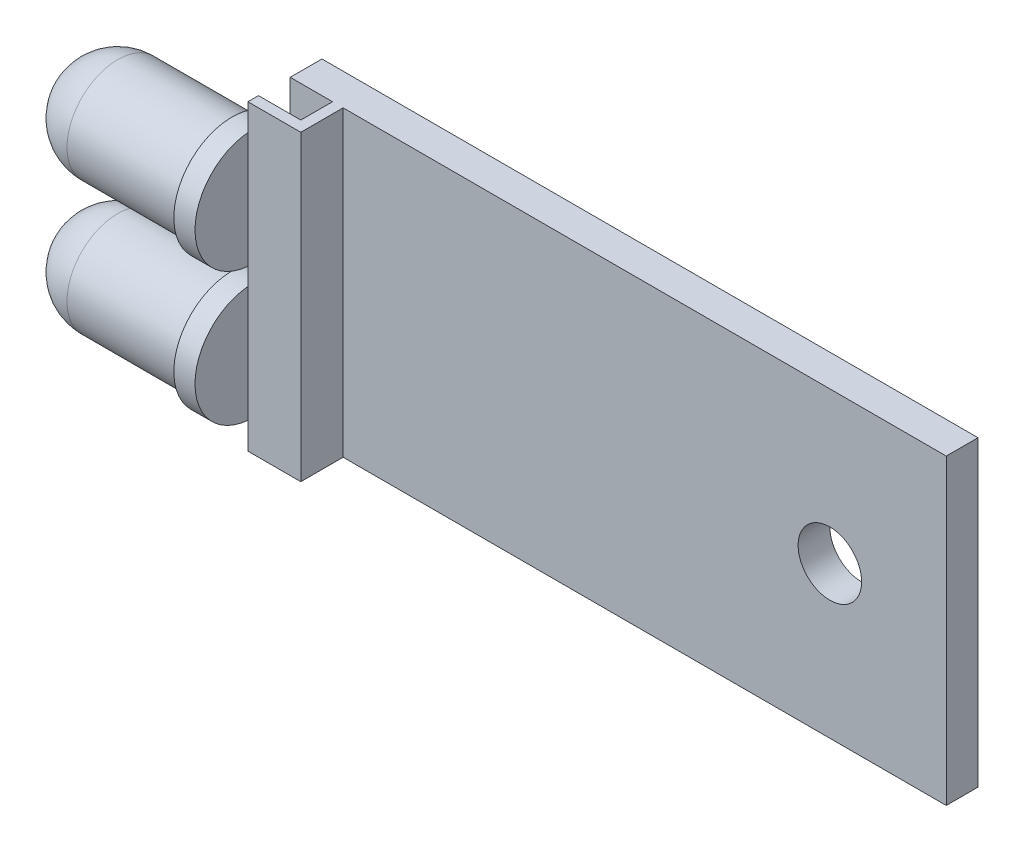
SolidWorks part; units mm, degrees
ref_plane "Front Plane" through (0, 0, 0) normal (0, 0, 1) x (1, 0, 0)
ref_plane "Top Plane" through (0, 0, 0) normal (0, 1, 0) x (1, 0, 0)
ref_plane "Right Plane" through (0, 0, 0) normal (1, 0, 0) x (0, 0, -1)
sketch "Sketch1" plane through (0, 0, 0) normal (0, 0, 1) x (1, 0, 0)
  line L1 (0, -7.15) -> (31, -7.15)
  line L2 (0, -7.15) -> (0, 7.15)
  line L3 (0, 7.15) -> (31, 7.15)
  line L4 (31, -7.15) -> (31, 7.15)
  point P6 (0, 0)
  dimension "D1" = 31
  dimension "D2" = 14.3
extrude "Boss-Extrude1" add sketch "Sketch1" along normal blind 1.5
sketch "Sketch2" plane through (0, -7.15, 0) normal (0, -1, 0) x (1, 0, 0)
  line L0 (2.5, 1.5) -> (2.5, 3.5)
  line L1 (0, 1.5) -> (31, 1.5) construction
  line L2 (2.5, 3.5) -> (0, 3.5)
  line L3 (2, 1.5) -> (2, 3)
  line L4 (2, 3) -> (0, 3)
  line L5 (0, 3) -> (0, 3.5)
  line L6 (2.5, 1.5) -> (2, 1.5)
  line L7 (0, 1.5) -> (0, 0) construction
  dimension "D1" = 0.5
  dimension "D2" = 0.5
  dimension "D3" = 2
  dimension "D4" = 2
extrude "Boss-Extrude2" add sketch "Sketch2" against normal through all
ref_plane "Plane1" through (0, -3.15, 0) normal (0, -1, 0) x (-1, 0, 0)
sketch "Sketch4" plane through (0, -3.15, 0) normal (0, -1, 0) x (1, 0, 0)
  line L0 (0, 3.5) -> (0, 6)
  line L1 (0, 6) -> (-1, 6)
  line L2 (-1, 6) -> (-1, 5.65)
  line L3 (-1, 5.65) -> (-6.4, 5.65)
  line L4 (0, 3.5) -> (0, 3) construction
  line L5 (0, 3.25) -> (-8.8, 3.25)
  line L6 (0, 3.5) -> (0, 3.25)
  arc A0 (-6.4, 5.65) -> (-8.8, 3.25) centre (-6.4, 3.25) ccw
  point P9 (0, 3.25)
  dimension "D1" = 2.75
  dimension "D2" = 1
  dimension "D3" = 2.4
  dimension "D4" = 8.8
revolve "Revolve1" add sketch "Sketch4" angle 360 about L5
mirror "Mirror1" about plane through (0, 0, 0) normal (0, 1, 0) of "Revolve1"
sketch "Sketch5" plane through (0, 0, 1.5) normal (0, 0, 1) x (1, 0, 0)
  line L0 (31, -7.15) -> (31, 7.15) construction
  circle A0 centre (25.5, 0) radius 1.5
  point P4 (31, 0)
  dimension "D1" = 3
  dimension "D2" = 5.5
extrude "Cut-Extrude1" cut sketch "Sketch5" against normal blind 1.5
